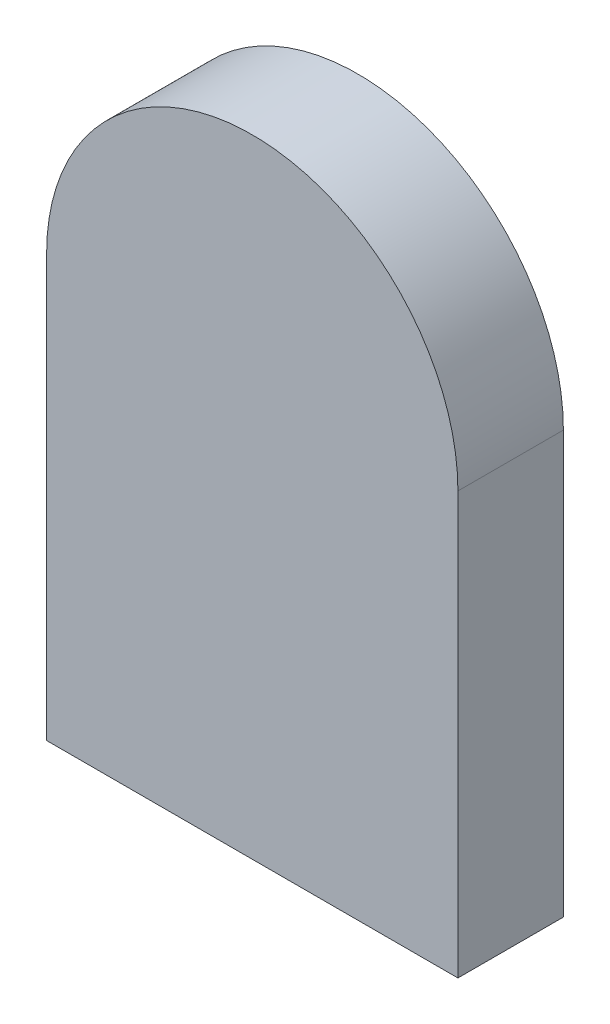
SolidWorks part; units mm, degrees
ref_plane "Alzado" through (0, 0, 0) normal (0, 0, 1) x (1, 0, 0)
ref_plane "Planta" through (0, 0, 0) normal (0, 1, 0) x (1, 0, 0)
ref_plane "Vista lateral" through (0, 0, 0) normal (1, 0, 0) x (0, 0, -1)
sketch "Croquis1" plane through (0, 0, 0) normal (0, 0, 1) x (1, 0, 0)
  line L0 (-77.3436, -6.8132) -> (-77.3436, 0.1868)
  line L1 (-78.3436, 0.1857) -> (-78.3436, -7.8132)
  line L2 (-71.5436, 0.1868) -> (-71.5436, -6.8132)
  line L5 (-70.5436, -7.8132) -> (-70.5436, 0.1857)
  line L6 (-77.3436, -6.8132) -> (-77.3436, -7.8132)
  line L7 (-77.3436, -7.8132) -> (-78.3436, -7.8132)
  line L8 (-71.5436, -6.8132) -> (-71.5436, -7.8132)
  line L9 (-71.5436, -7.8132) -> (-70.5436, -7.8132)
  arc A0 (-77.3436, 0.1868) -> (-71.5436, 0.1868) centre (-74.4436, 0.1868) cw
  arc A1 (-78.3436, 0.1857) -> (-70.5436, 0.1857) centre (-74.4436, 0.1857) cw
  dimension "D1" = 1
  dimension "D3" = 7
  dimension "D4" = 5.8
  dimension "D5" = 1
extrude "Saliente-Extruir1" add sketch "Croquis1" along normal blind 1
sketch "Croquis3" plane through (0, 0, 1) normal (0, 0, 1) x (1, 0, 0)
  line L0 (-77.3436, -7.8132) -> (-78.3436, -7.8132)
  line L1 (-78.3436, -7.8132) -> (-78.3436, 0.1857)
  line L2 (-70.5436, -7.8132) -> (-77.3436, -7.8132)
  line L6 (-70.5436, -7.8132) -> (-70.5436, 0.1857)
  arc A1 (-78.3436, 0.1857) -> (-70.5436, 0.1857) centre (-74.4436, 0.1857) cw
extrude "Saliente-Extruir2" add sketch "Croquis3" along normal blind 1
